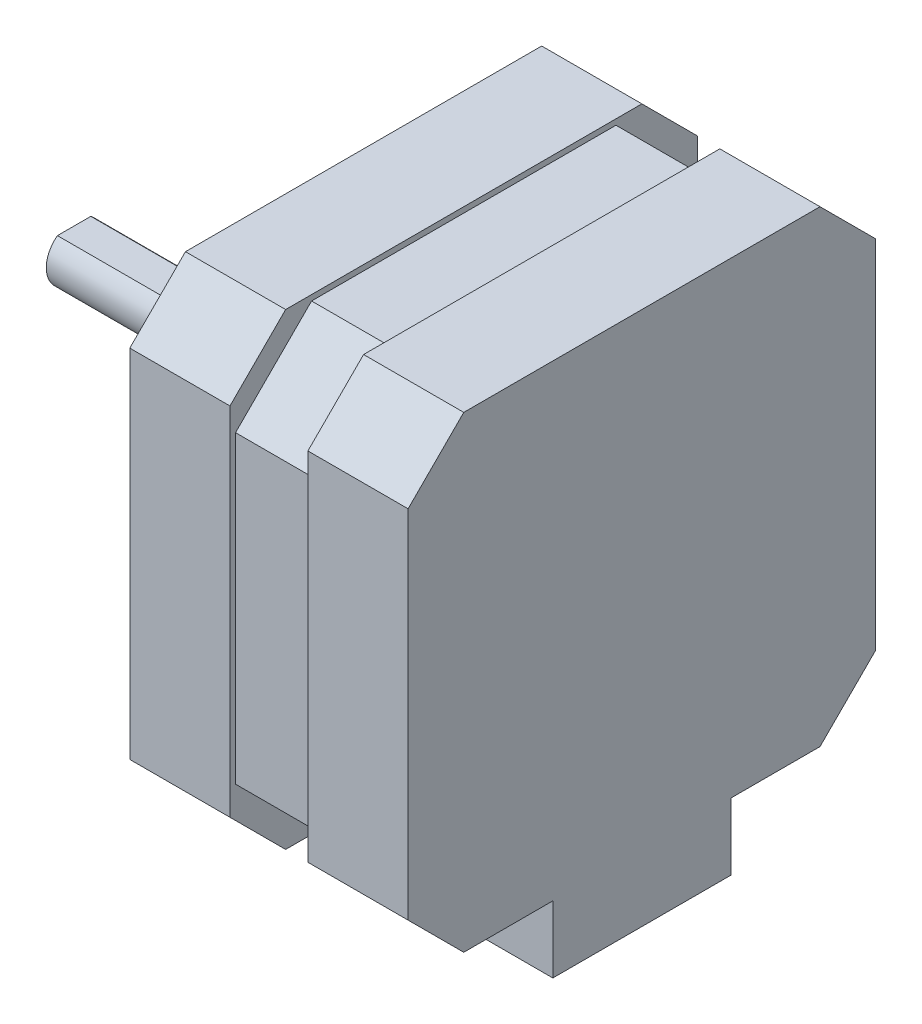
SolidWorks part; units mm, degrees
ref_plane "Front Plane" through (0, 0, 0) normal (0, 0, 1) x (1, 0, 0)
ref_plane "Top Plane" through (0, 0, 0) normal (0, 1, 0) x (1, 0, 0)
ref_plane "Right Plane" through (0, 0, 0) normal (1, 0, 0) x (0, 0, -1)
sketch "Sketch1" plane through (0, 0, 0) normal (1, 0, 0) x (0, 0, -1)
  line L0 (-21, 16) -> (-16, 21)
  line L1 (-16, 21) -> (16, 21)
  line L2 (16, 21) -> (21, 16)
  line L3 (21, 16) -> (21, -16)
  line L4 (21, -16) -> (16, -21)
  line L5 (16, -21) -> (-16, -21)
  line L6 (-16, -21) -> (-21, -16)
  line L7 (-21, -16) -> (-21, 16)
  point P9 (21, 0)
  point P11 (0, 21)
  dimension "D1" = 42
  dimension "D2" = 32
extrude "Boss-Extrude1" add sketch "Sketch1" along normal mid plane 25
sketch "Sketch2" plane through (0, 0, 0) normal (1, 0, 0) x (0, 0, -1)
  line L1 (-21, 16) -> (-21, -16) construction
  line L2 (-21, -13.6716) -> (-20.5, -13.6716)
  line L3 (-20.5, -13.6716) -> (-13.6716, -20.5)
  line L4 (-13.6716, -20.5) -> (-13.6716, -21)
  line L5 (-16, -21) -> (16, -21) construction
  line L7 (13.6716, -21) -> (13.6716, -20.5)
  line L8 (13.6716, -20.5) -> (20.5, -13.6716)
  line L10 (20.5, -13.6716) -> (21, -13.6716)
  line L11 (21, -16) -> (21, 16) construction
  line L13 (21, 13.6716) -> (20.5, 13.6716)
  line L14 (20.5, 13.6716) -> (13.6716, 20.5)
  line L15 (13.6716, 20.5) -> (13.6716, 21)
  line L16 (16, 21) -> (-16, 21) construction
  line L18 (-13.6716, 21) -> (-13.6716, 20.5)
  line L19 (-13.6716, 20.5) -> (-20.5, 13.6716)
  line L20 (-20.5, 13.6716) -> (-21, 13.6716)
  line L21 (-16, 21) -> (-21, 16) construction
  line L22 (-13.6716, 21) -> (-16, 21)
  line L23 (-16, 21) -> (-21, 16)
  line L24 (-21, 16) -> (-21, 13.6716)
  line L25 (-21, -13.6716) -> (-21, -16)
  line L26 (-21, -16) -> (-16, -21)
  line L27 (-16, -21) -> (-13.6716, -21)
  line L28 (13.6716, -21) -> (16, -21)
  line L29 (16, -21) -> (21, -16)
  line L30 (21, -16) -> (21, -13.6716)
  line L31 (21, 13.6716) -> (21, 16)
  line L32 (21, 16) -> (16, 21)
  line L33 (16, 21) -> (13.6716, 21)
  dimension "D1" = 0.5
  dimension "D2" = 2
extrude "Cut-Extrude1" cut sketch "Sketch2" against normal mid plane 7
sketch "Sketch4" plane through (0, 0, 21) normal (0, 0, 1) x (1, 0, 0)
  line L1 (-3.5, 13.6716) -> (3.5, 13.6716)
  line L2 (-3.5, 13.6716) -> (-3.5, -13.6716)
  line L3 (-3.5, -13.6716) -> (3.5, -13.6716)
  line L4 (3.5, 13.6716) -> (3.5, -13.6716)
extrude "Cut-Extrude2" cut sketch "Sketch4" against normal up to vertex (0.5 mm away)
sketch "Sketch5" plane through (0, 21, 0) normal (0, 1, 0) x (1, 0, 0)
  line L1 (-3.5, 13.6716) -> (3.5, 13.6716)
  line L2 (-3.5, 13.6716) -> (-3.5, -13.6716)
  line L3 (-3.5, -13.6716) -> (3.5, -13.6716)
  line L4 (3.5, 13.6716) -> (3.5, -13.6716)
extrude "Cut-Extrude3" cut sketch "Sketch5" against normal up to vertex (0.5 mm away)
sketch "Sketch6" plane through (0, 0, -21) normal (0, 0, -1) x (-1, 0, 0)
  line L1 (-3.5, 13.6716) -> (3.5, 13.6716)
  line L2 (-3.5, 13.6716) -> (-3.5, -13.6716)
  line L3 (-3.5, -13.6716) -> (3.5, -13.6716)
  line L4 (3.5, 13.6716) -> (3.5, -13.6716)
extrude "Cut-Extrude4" cut sketch "Sketch6" against normal up to vertex (0.5 mm away)
sketch "Sketch7" plane through (0, -21, 0) normal (0, -1, 0) x (1, 0, 0)
  line L1 (-3.5, 13.6716) -> (3.5, 13.6716)
  line L2 (-3.5, 13.6716) -> (-3.5, -13.6716)
  line L3 (-3.5, -13.6716) -> (3.5, -13.6716)
  line L4 (3.5, 13.6716) -> (3.5, -13.6716)
extrude "Cut-Extrude5" cut sketch "Sketch7" against normal up to vertex (0.5 mm away) up to point (-3.5, -20.5, 13.6716)
sketch "Sketch8" plane through (-12.5, 0, 0) normal (-1, 0, 0) x (0, 0, 1)
  circle A0 centre (0, 0) radius 11
  dimension "D1" = 22
extrude "Boss-Extrude2" add sketch "Sketch8" along normal blind 2
sketch "Sketch9" plane through (-14.5, 0, 0) normal (-1, 0, 0) x (0, 0, 1)
  circle A0 centre (0, 0) radius 2.5
  dimension "D1" = 5
extrude "Boss-Extrude3" add sketch "Sketch9" along normal blind 24
hole_wizard "M3 Tapped Hole1" positions "Sketch10" profile "Sketch11" tap size "M3" standard "DIN"
sketch "Sketch10" plane through (-12.5, 0, 0) normal (-1, 0, 0) x (0, 0, 1)
  line L1 (-15.5, -15.5) -> (15.5, -15.5) construction
  line L2 (-15.5, -15.5) -> (-15.5, 15.5) construction
  line L3 (-15.5, 15.5) -> (15.5, 15.5) construction
  line L4 (15.5, -15.5) -> (15.5, 15.5) construction
  line L5 (-15.5, -15.5) -> (15.5, 15.5) construction
  line L6 (-15.5, 15.5) -> (15.5, -15.5) construction
  point P0 (-15.5, 15.5)
  point P2 (15.5, 15.5)
  point P4 (-15.5, -15.5)
  point P6 (15.5, -15.5)
  dimension "D1" = 31
sketch "Sketch11" plane through (-12.5, 15.5, -15.5) normal (0, 1, 0) x (0, 0, 1)
  line L0 (0, 0) -> (0, 6.7511)
  line L1 (0, 6.7511) -> (1.25, 6)
  line L2 (1.25, 6) -> (1.25, 0)
  line L5 (1.25, 0) -> (0, 0)
  line L10 (0, 6.7511) -> (-1.25, 6) construction
  line L11 (0, -6.35) -> (0, 107.95) construction
  dimension "Tap Drill Dia." = 2.5
  dimension "Tap Drill Depth" = 6
  dimension "Drill Angle" = 118
cosmetic thread "Hole Thread1" parameters "D1"=4.5, "D2"=3
cosmetic thread "Hole Thread2" parameters "D1"=4.5, "D2"=3
cosmetic thread "Hole Thread3" parameters "D1"=4.5, "D2"=3
cosmetic thread "Hole Thread4" parameters "D1"=4.5, "D2"=3
sketch "Sketch12" plane through (-38.5, 0, 0) normal (-1, 0, 0) x (0, 0, 1)
  line L1 (-1.5, 2) -> (1.5, 2)
  line L2 (-1.5, 2) -> (-1.5, 2.5)
  line L3 (-1.5, 2.5) -> (1.5, 2.5)
  line L4 (1.5, 2) -> (1.5, 2.5)
  circle A0 centre (0, 0) radius 2.5 construction
  circle A1 centre (0, 0) radius 2.5 construction
  dimension "D1" = 0.5
extrude "Cut-Extrude6" cut sketch "Sketch12" against normal blind 20
sketch "Sketch13" plane through (0, -21, 0) normal (0, -1, 0) x (1, 0, 0)
  line L0 (12.5, 16) -> (12.5, -16) construction
  line L1 (12.5, 8) -> (3.5, 8)
  line L2 (12.5, 8) -> (12.5, -8)
  line L3 (12.5, -8) -> (3.5, -8)
  line L4 (3.5, 8) -> (3.5, -8)
  line L5 (0, 0) -> (3.5, 0) construction
  dimension "D1" = 16
  dimension "D2" = 9
extrude "Boss-Extrude4" add sketch "Sketch13" along normal blind 6
